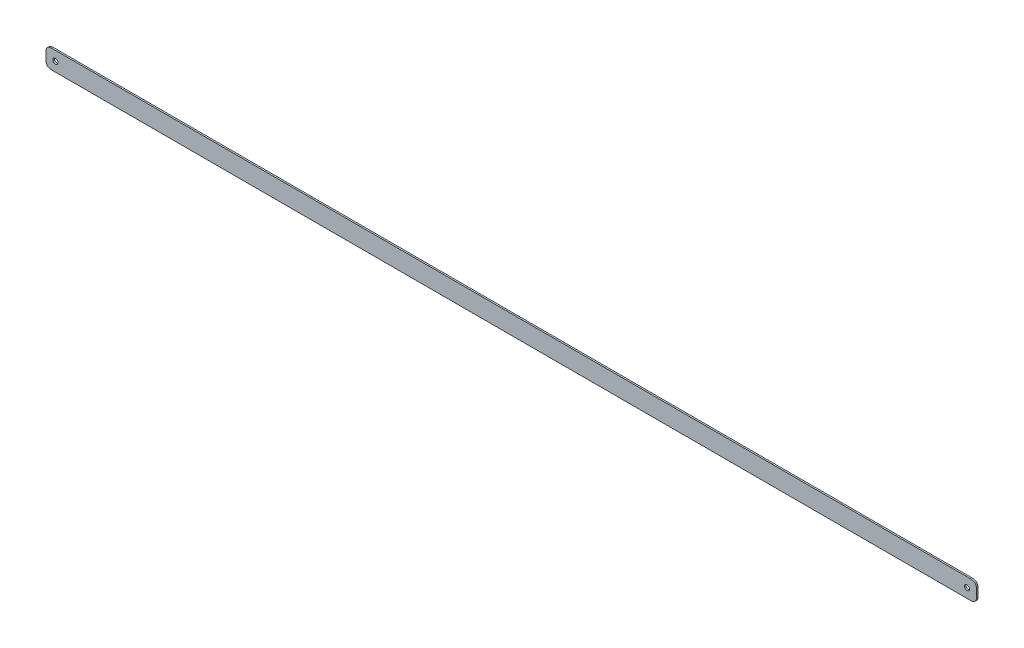
SolidWorks part; units mm, degrees
ref_plane "Front" through (0, 0, 0) normal (0, 0, 1) x (1, 0, 0)
ref_plane "Top" through (0, 0, 0) normal (0, 1, 0) x (1, 0, 0)
ref_plane "Right" through (0, 0, 0) normal (1, 0, 0) x (0, 0, -1)
sketch "Sketch1" plane through (0, 0, 0) normal (0, 0, 1) x (1, 0, 0)
  line L0 (0, 0) -> (924.6744, 0) construction
  line L1 (0, 0) -> (-9.525, 0) construction
  line L2 (-4.445, 9.525) -> (929.1194, 9.525)
  line L3 (-9.525, 4.445) -> (-9.525, -4.445)
  line L4 (-4.445, -9.525) -> (929.1194, -9.525)
  line L5 (934.1994, 4.445) -> (934.1994, -4.445)
  line L6 (-9.525, 9.525) -> (934.1994, -9.525) construction
  line L7 (-9.525, -9.525) -> (934.1994, 9.525) construction
  line L8 (924.6744, 0) -> (934.1994, 0) construction
  circle A0 centre (0, 0) radius 2.54
  circle A1 centre (924.6744, 0) radius 2.54
  arc A2 (-9.525, -4.445) -> (-4.445, -9.525) centre (-4.445, -4.445) ccw
  arc A3 (-4.445, 9.525) -> (-9.525, 4.445) centre (-4.445, 4.445) ccw
  arc A4 (929.1194, -9.525) -> (934.1994, -4.445) centre (929.1194, -4.445) ccw
  arc A5 (929.1194, 9.525) -> (934.1994, 4.445) centre (929.1194, 4.445) cw
  point P9 (462.3372, 0)
  dimension "D1" = 5.08
  dimension "D2" = 5.08
  dimension "D7" = 5.08
  dimension "D8" = 5.08
  dimension "D3" = 924.6744
  dimension "D4" = 19.05
  dimension "D5" = 9.525
  dimension "D6" = 9.525
extrude "Boss-Extrude1" add sketch "Sketch1" along normal blind 1.5875
